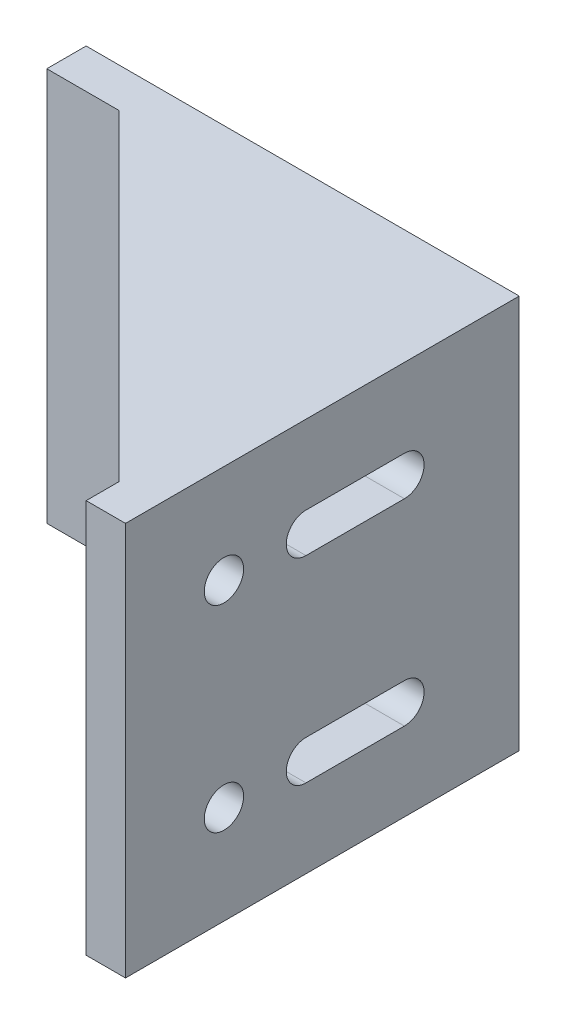
SolidWorks part; units mm, degrees
ref_plane "Front Plane" through (0, 0, 0) normal (0, 0, 1) x (1, 0, 0)
ref_plane "Top Plane" through (0, 0, 0) normal (0, 1, 0) x (1, 0, 0)
ref_plane "Right Plane" through (0, 0, 0) normal (1, 0, 0) x (0, 0, -1)
sketch "Sketch1" plane through (0, 0, 0) normal (0, 0, 1) x (1, 0, 0)
  line L0 (0, 0) -> (0, 60)
  line L1 (0, 60) -> (60, 60)
  line L2 (60, 60) -> (60, 0)
  line L3 (60, 0) -> (0, 0)
  line L4 (0, 30) -> (60, 30) construction
  line L5 (15, 45) -> (55, 45) construction
  line L6 (27.5, 42) -> (42.5, 42)
  line L7 (27.5, 48) -> (42.5, 48)
  line L8 (27.5, 12) -> (42.5, 12)
  line L9 (27.5, 18) -> (42.5, 18)
  circle A0 centre (15, 45) radius 3
  arc A1 (27.5, 48) -> (27.5, 42) centre (27.5, 45) ccw
  arc A2 (42.5, 42) -> (42.5, 48) centre (42.5, 45) ccw
  arc A3 (27.5, 12) -> (27.5, 18) centre (27.5, 15) cw
  arc A4 (42.5, 18) -> (42.5, 12) centre (42.5, 15) cw
  circle A5 centre (15, 15) radius 3
  point P11 (35, 45)
  dimension "D3" = 6
  dimension "D6" = 6
  dimension "D1" = 60
  dimension "D2" = 60
  dimension "D4" = 15
  dimension "D5" = 15
  dimension "D7" = 15
  dimension "D8" = 12.5
  dimension "D9" = 20
extrude "Boss-Extrude1" add sketch "Sketch1" along normal blind 6
sketch "Sketch2" plane through (60, 0, 0) normal (1, 0, 0) x (0, 0, -1)
  line L0 (0, 0) -> (-60, 0)
  line L1 (-60, 0) -> (-60, 60)
  line L2 (0, 0) -> (0, 60)
  line L3 (0, 60) -> (-60, 60)
  line L4 (-60, 30) -> (0, 30) construction
  line L5 (-45, 45) -> (-6.5182, 45) construction
  line L6 (-32.5, 48) -> (-17.5, 48)
  line L7 (-32.5, 42) -> (-17.5, 42)
  line L8 (-32.5, 18) -> (-17.5, 18)
  line L9 (-32.5, 12) -> (-17.5, 12)
  circle A0 centre (-45, 45) radius 3
  arc A1 (-32.5, 48) -> (-32.5, 42) centre (-32.5, 45) ccw
  arc A2 (-17.5, 42) -> (-17.5, 48) centre (-17.5, 45) ccw
  arc A3 (-32.5, 12) -> (-32.5, 18) centre (-32.5, 15) cw
  arc A4 (-17.5, 18) -> (-17.5, 12) centre (-17.5, 15) cw
  circle A5 centre (-45, 15) radius 3
  dimension "D2" = 6
  dimension "D1" = 60
  dimension "D3" = 15
  dimension "D4" = 15
  dimension "D5" = 15
  dimension "D6" = 12.5
extrude "Boss-Extrude2" add sketch "Sketch2" along normal blind 6
sketch "Sketch3" plane through (0, 60, 0) normal (0, 1, 0) x (1, 0, 0)
  line L0 (66, 0) -> (11, 0)
  line L1 (66, 0) -> (0, 0) construction
  line L2 (11, 0) -> (11, -6)
  line L3 (60, -6) -> (0, -6) construction
  line L4 (11, -6) -> (60, -55)
  line L5 (60, -6) -> (60, -60) construction
  line L6 (60, -55) -> (66, -55)
  line L7 (66, 0) -> (66, -60) construction
  line L8 (66, -55) -> (66, 0)
  dimension "D1" = 55
  dimension "D2" = 55
extrude "Boss-Extrude3" add sketch "Sketch3" against normal blind 3
sketch "Sketch4" plane through (0, 0, 0) normal (0, -1, 0) x (1, 0, 0)
  line L0 (66, 0) -> (66, 55)
  line L1 (66, 60) -> (66, 0) construction
  line L2 (66, 55) -> (60, 55)
  line L3 (60, 60) -> (60, 6) construction
  line L4 (60, 55) -> (11, 6)
  line L5 (60, 55) -> (11, 6) construction
  line L6 (11, 6) -> (11, 0)
  line L7 (0, 0) -> (66, 0) construction
  line L8 (11, 0) -> (66, 0)
  dimension "D1" = 55
  dimension "D2" = 55
extrude "Boss-Extrude4" add sketch "Sketch4" against normal blind 3
